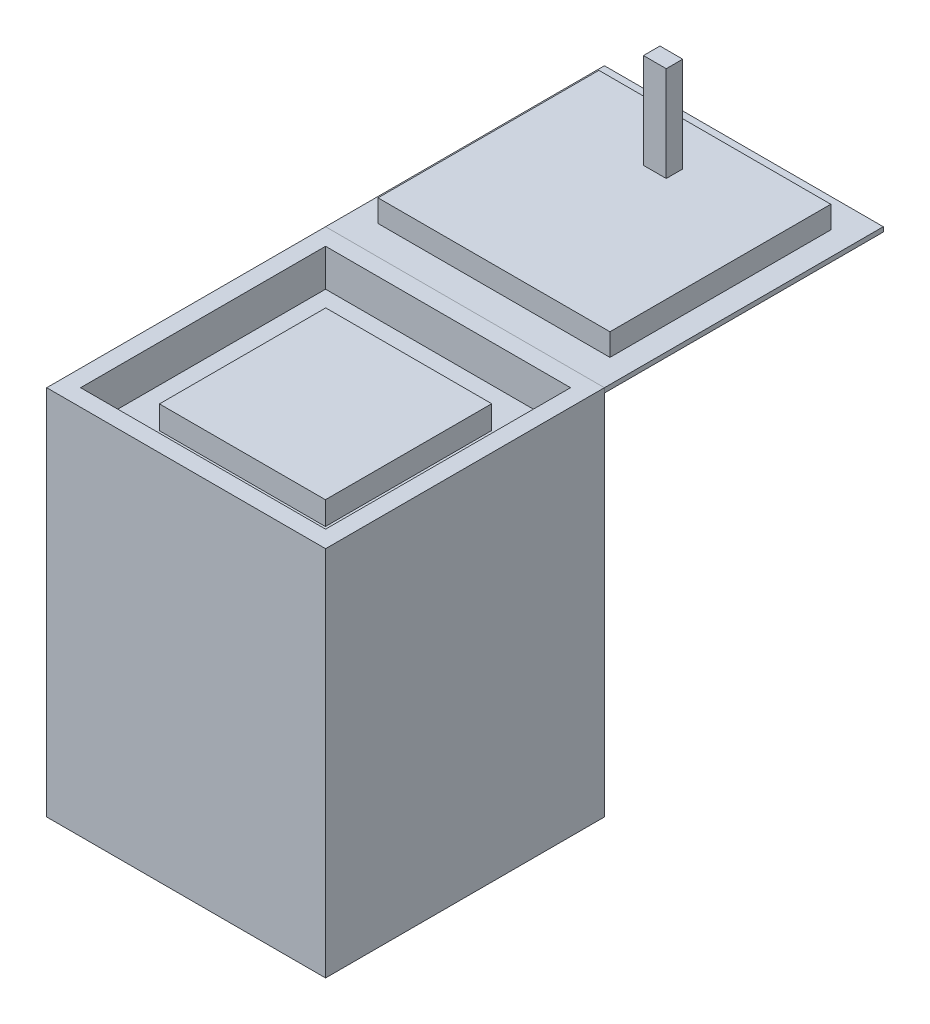
SolidWorks part; units mm, degrees
ref_plane "Front Plane" through (0, 0, 0) normal (0, 0, 1) x (1, 0, 0)
ref_plane "Top Plane" through (0, 0, 0) normal (0, 1, 0) x (1, 0, 0)
ref_plane "Right Plane" through (0, 0, 0) normal (1, 0, 0) x (0, 0, -1)
other "Center of Mass"
sketch "Sketch1" plane through (0, 0, 0) normal (0, 1, 0) x (1, 0, 0)
  line L1 (300, 300) -> (-300, 300)
  line L2 (300, 300) -> (300, -300)
  line L3 (300, -300) -> (-300, -300)
  line L4 (-300, 300) -> (-300, -300)
  line L5 (300, 300) -> (-300, -300) construction
  line L6 (300, -300) -> (-300, 300) construction
  point P0 (0, 0)
  dimension "D1" = 600
  dimension "D2" = 600
extrude "Boss-Extrude1" add sketch "Sketch1" along normal blind 800
sketch "Sketch2" plane through (0, 800, 0) normal (0, 1, 0) x (1, 0, 0)
  line L1 (-263.5729, -263.5729) -> (263.5729, -263.5729)
  line L2 (-263.5729, -263.5729) -> (-263.5729, 263.5729)
  line L3 (-263.5729, 263.5729) -> (263.5729, 263.5729)
  line L4 (263.5729, -263.5729) -> (263.5729, 263.5729)
  line L5 (-263.5729, -263.5729) -> (263.5729, 263.5729) construction
  line L6 (-263.5729, 263.5729) -> (263.5729, -263.5729) construction
extrude "Cut-Extrude2" cut sketch "Sketch2" against normal blind 80
sketch "Sketch3" plane through (0, 720, 0) normal (0, 1, 0) x (1, 0, 0)
  line L1 (-178.5595, -178.9117) -> (178.5595, -178.9117)
  line L2 (-178.5595, -178.9117) -> (-178.5595, 178.9117)
  line L3 (-178.5595, 178.9117) -> (178.5595, 178.9117)
  line L4 (178.5595, -178.9117) -> (178.5595, 178.9117)
  line L5 (-178.5595, -178.9117) -> (178.5595, 178.9117) construction
  line L6 (-178.5595, 178.9117) -> (178.5595, -178.9117) construction
extrude "Boss-Extrude2" add sketch "Sketch3" along normal blind 50
sketch "Sketch4" plane through (0, 800, 0) normal (0, 1, 0) x (1, 0, 0)
  line L1 (300, 300) -> (-300, 300)
  line L2 (300, 300) -> (300, 900)
  line L3 (300, 900) -> (-300, 900)
  line L4 (-300, 300) -> (-300, 900)
  dimension "D1" = 600
  dimension "D2" = 600
extrude "Boss-Extrude3" add sketch "Sketch4" against normal blind 10 separate body
sketch "Sketch7" plane through (0, 0, 0) normal (1, 0, 0) x (0, 0, -1)
  line L0 (600, 533.3011) -> (600, 1035.5411) construction
  line L1 (300, 800) -> (300, 0) construction
  line L2 (362.4057, 800) -> (362.4057, 847.8347)
  line L3 (362.4057, 800) -> (837.5943, 800)
  line L5 (362.4057, 847.8347) -> (837.5943, 847.8347)
  line L6 (837.5943, 800) -> (837.5943, 847.8347)
  line L7 (900, 800) -> (300, 800) construction
  dimension "D1" = 300
  dimension "D2" = 47.8347
  dimension "D3" = 0
extrude "Boss-Extrude8" add sketch "Sketch7" along normal mid plane 499 separate body
ref_plane "Plane1" through (0, 540, 0) normal (0, -1, 0) x (-1, 0, 0)
sketch "Sketch15" plane through (0, 0, 0) normal (1, 0, 0) x (0, 0, -1)
  line L1 (743.9858, 847.8347) -> (708.4776, 847.8347)
  line L2 (743.9858, 847.8347) -> (743.9858, 1052.5)
  line L3 (743.9858, 1052.5) -> (708.4776, 1052.5)
  line L4 (708.4776, 847.8347) -> (708.4776, 1052.5)
  line L6 (837.5943, 847.8347) -> (362.4057, 847.8347) construction
  dimension "D1" = 204.6653
  dimension "D2" = 0
extrude "Boss-Extrude9" add sketch "Sketch15" along normal mid plane 49
ref_plane "Plane2" through (0, 390, 0) normal (0, 1, 0) x (1, 0, 0)
ref_plane "Plane3" through (0, 0, -10) normal (0, 0, 1) x (1, 0, 0)
sketch "Sketch16" plane through (0, 390, 0) normal (0, 1, 0) x (1, 0, 0)
  line L0 (397.3929, 10) -> (-433.356, 10) construction
  line L1 (-330, 10) -> (330, 10) construction
sketch "Sketch17" plane through (0, 0, -10) normal (0, 0, 1) x (1, 0, 0)
  line L0 (432.5531, 390) -> (-527.396, 390) construction
  line L1 (456.9119, 390) -> (-456.9119, 390) construction
sketch "Sketch18" plane through (0, 0, -10) normal (0, 0, 1) x (1, 0, 0)
  line L0 (460.5739, 390) -> (-561.2855, 390) construction
  line L1 (527.972, 390) -> (-527.972, 390) construction
sketch "Sketch19" plane through (0, 0, -10) normal (0, 0, 1) x (1, 0, 0)
  line L0 (0, 1147.3935) -> (0, -150.6808)
  line L1 (0, -578.875) -> (0, 578.875) construction
ref_point "Point2"
